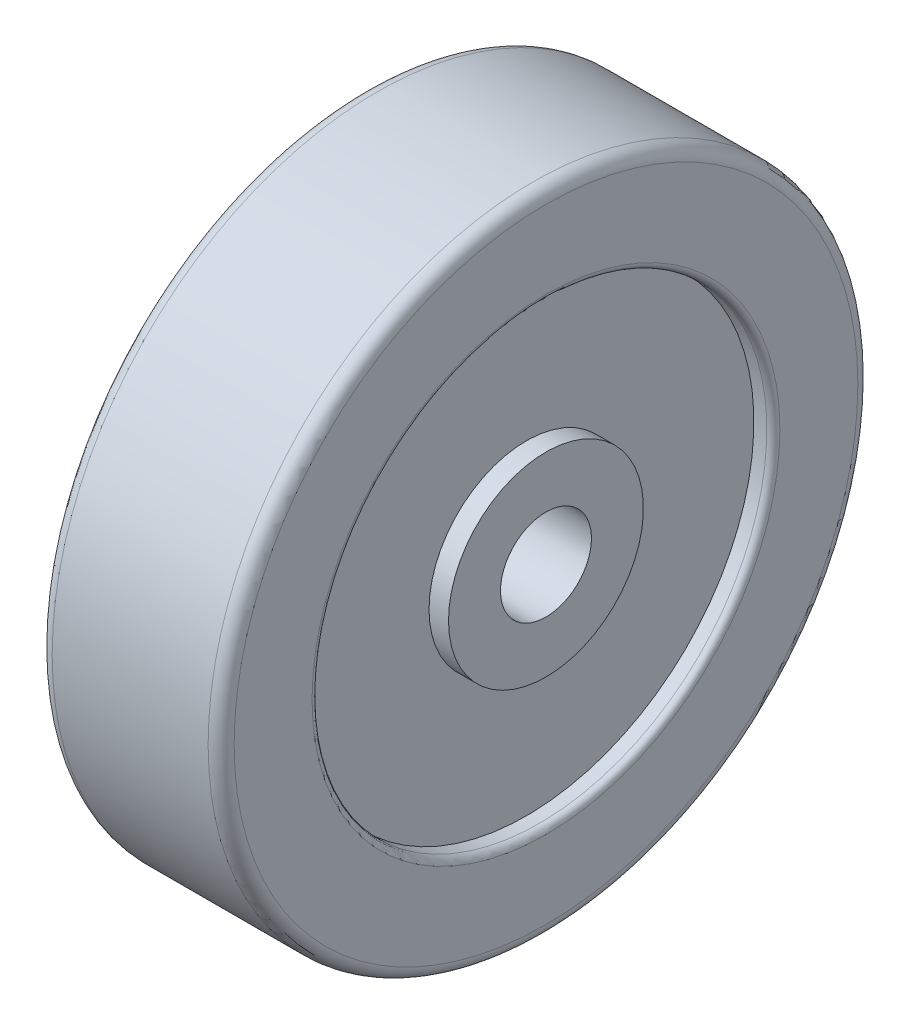
SolidWorks part; units mm, degrees
ref_plane "Alzado" through (0, 0, 0) normal (0, 0, 1) x (1, 0, 0)
ref_plane "Planta" through (0, 0, 0) normal (0, 1, 0) x (1, 0, 0)
ref_plane "Vista lateral" through (0, 0, 0) normal (1, 0, 0) x (0, 0, -1)
sketch "Croquis1" plane through (0, 0, 0) normal (0, 0, 1) x (1, 0, 0)
  line L0 (-12.6497, 0) -> (15.3503, 0)
  line L1 (15.3503, 0) -> (15.3503, 8)
  line L2 (15.3503, 8) -> (12.3503, 8)
  line L3 (12.3503, 8) -> (12.3503, 28)
  line L4 (12.3503, 28) -> (15.3503, 28)
  line L5 (15.3503, 28) -> (15.3503, 43)
  line L6 (15.3503, 43) -> (-12.6497, 43)
  line L7 (-12.6497, 43) -> (-12.6497, 28)
  line L8 (-12.6497, 28) -> (-9.6497, 28)
  line L9 (-9.6497, 28) -> (-9.6497, 8)
  line L10 (-9.6497, 8) -> (-12.6497, 8)
  line L11 (-12.6497, 8) -> (-12.6497, 0)
  line L12 (-30.1637, -7) -> (43.7885, -7) construction
  point P3 (1.3503, 0)
  point P14 (1.3503, 43)
  point P17 (0, 0)
  point P18 (0, 0)
  dimension "D1" = 28
  dimension "D2" = 7
  dimension "D3" = 50
  dimension "D4" = 35
  dimension "D5" = 15
  dimension "D6" = 3
revolve "Revolución1" add sketch "Croquis1" angle 360 about L12
fillet "Redondeo1" radius 2 1 edges at (15.3503, -7, 50)
fillet "Redondeo2" radius 2 1 edges at (-12.6497, -7, 50)
fillet "Redondeo3" radius 1 1 edges at (-12.6497, -7, 35)
fillet "Redondeo4" radius 1 1 edges at (15.3503, -7, 35)
